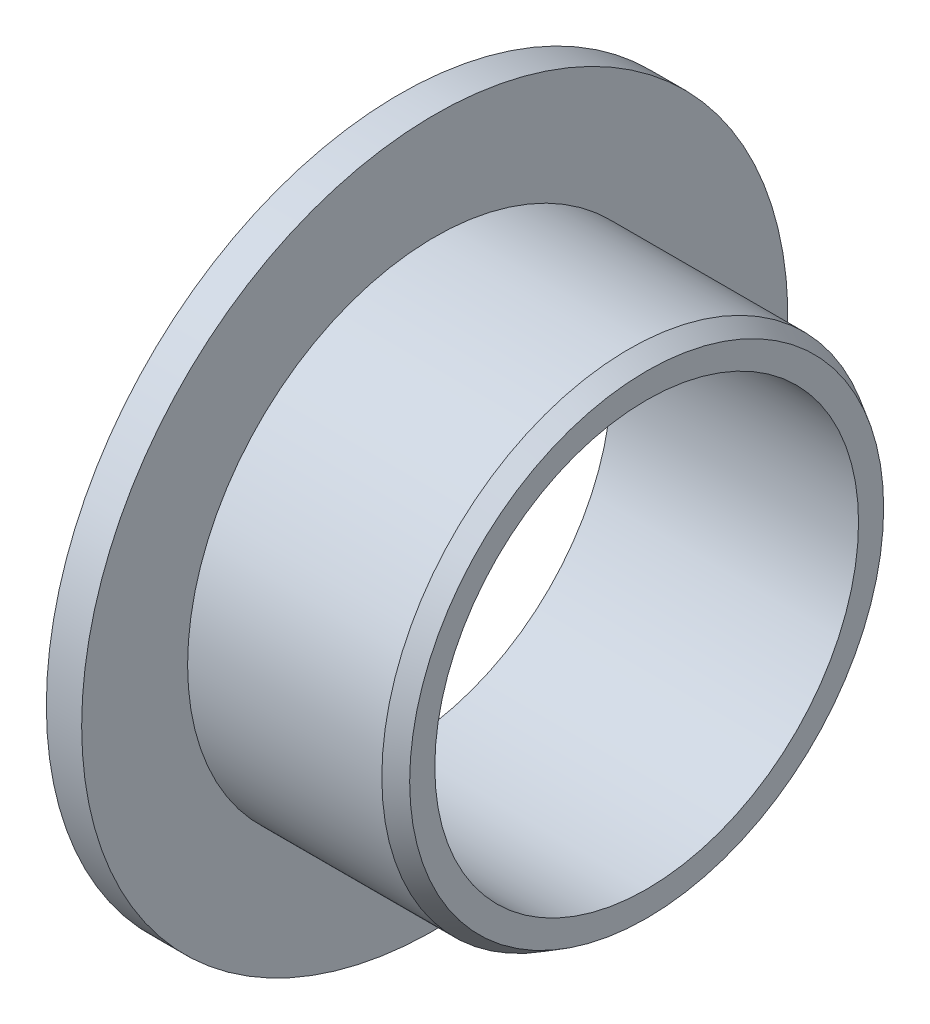
SolidWorks part; units mm, degrees
ref_plane "Płaszczyzna przednia" through (0, 0, 0) normal (0, 0, 1) x (1, 0, 0)
ref_plane "Płaszczyzna górna" through (0, 0, 0) normal (0, 1, 0) x (1, 0, 0)
ref_plane "Płaszczyzna prawa" through (0, 0, 0) normal (1, 0, 0) x (0, 0, -1)
sketch "Szkic1" plane through (0, 0, 0) normal (0, 0, 1) x (1, 0, 0)
  line L0 (0, 0) -> (0, 6) construction
  line L1 (0, 6) -> (7, 6)
  line L2 (0, 0) -> (24.2255, 0) construction
  line L3 (7, 6) -> (7, 7)
  line L4 (7, 7) -> (1, 7)
  line L5 (0, 6) -> (0, 10)
  line L6 (0, 10) -> (1, 10)
  line L7 (1, 10) -> (1, 7)
  point P10 (1, 8.5)
  dimension "D1" = 6
  dimension "D2" = 7
  dimension "D3" = 10
  dimension "D4" = 1
  dimension "D5" = 7
revolve "Obrót1" add sketch "Szkic1" angle 360 about L2
chamfer "Sfazowanie1" distance 0.5 angle 30 1 edges at (7, 0, 7)
